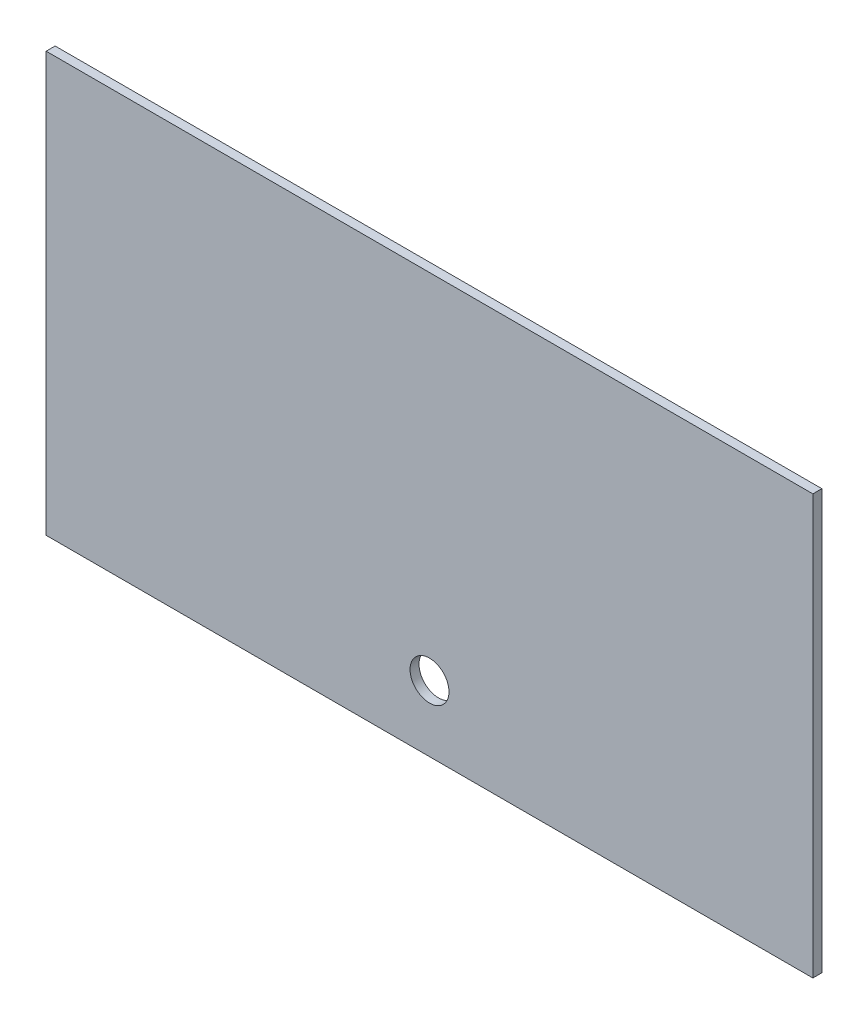
SolidWorks part; units mm, degrees
ref_plane "Front Plane" through (0, 0, 0) normal (0, 0, 1) x (1, 0, 0)
ref_plane "Top Plane" through (0, 0, 0) normal (0, 1, 0) x (1, 0, 0)
ref_plane "Right Plane" through (0, 0, 0) normal (1, 0, 0) x (0, 0, -1)
sketch "Sketch1" plane through (0, 0, 0) normal (0, 0, 1) x (1, 0, 0)
  line L1 (-64, -35) -> (64, -35)
  line L2 (-64, -35) -> (-64, 35)
  line L3 (-64, 35) -> (64, 35)
  line L4 (64, -35) -> (64, 35)
  line L5 (-64, -35) -> (64, 35) construction
  line L6 (-64, 35) -> (64, -35) construction
  point P0 (0, 0)
  dimension "D1" = 128
  dimension "D2" = 70
extrude "Boss-Extrude1" add sketch "Sketch1" along normal blind 1.5
sketch "Sketch3" plane through (0, 0, 0) normal (0, 0, -1) x (-1, 0, 0)
  line L0 (64, 35) -> (64, -35) construction
  line L1 (64, -35) -> (-64, -35) construction
  circle A0 centre (0, -24) radius 3.25
  dimension "D1" = 6.5
  dimension "D2" = 64
  dimension "D3" = 11
extrude "Cut-Extrude1" cut sketch "Sketch3" against normal through all
